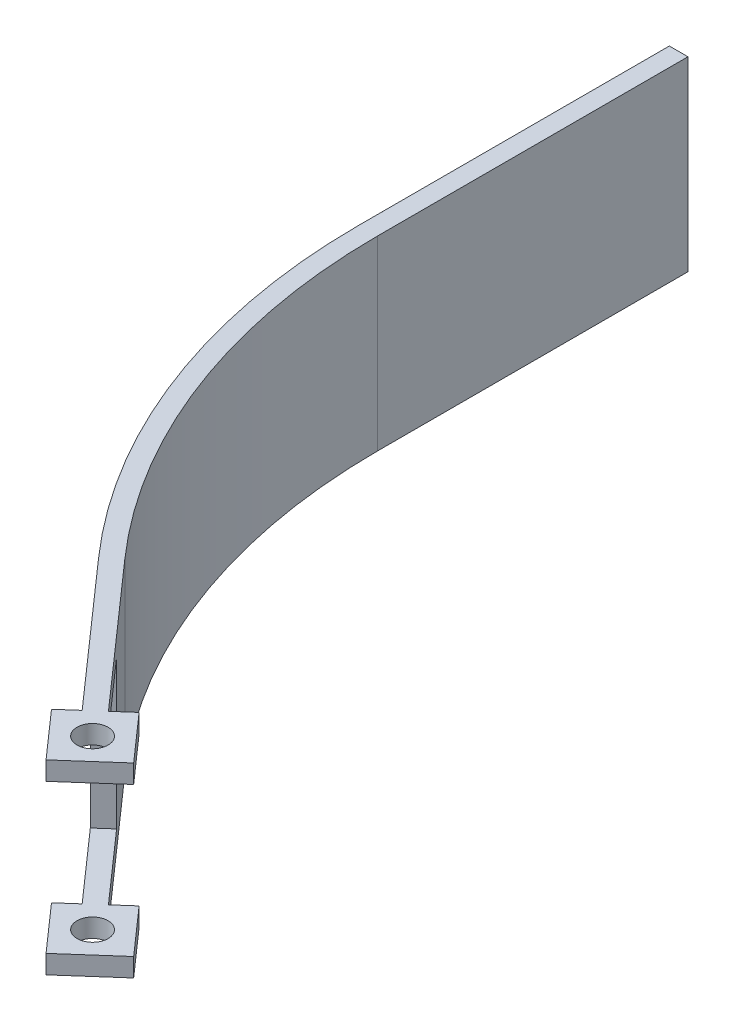
SolidWorks part; units mm, degrees
ref_plane "Face" through (0, 0, 0) normal (0, 0, 1) x (1, 0, 0)
ref_plane "Dessus" through (0, 0, 0) normal (0, 1, 0) x (1, 0, 0)
ref_plane "Droite" through (0, 0, 0) normal (1, 0, 0) x (0, 0, -1)
sketch "Esquisse1" plane through (0, 0, 0) normal (0, 1, 0) x (1, 0, 0)
  line L0 (0, 0) -> (0, 50)
  line L1 (0, 50) -> (3, 50)
  line L2 (3, 50) -> (3, 0)
  line L3 (25.5397, -67.5117) -> (27.7886, -65.526) construction
  line L4 (47.6449, -88.0144) -> (50.2686, -85.6978)
  line L5 (25.5397, -67.5117) -> (45.3961, -90)
  line L6 (27.7886, -65.526) -> (47.6449, -88.0144)
  line L7 (50.2686, -85.6978) -> (56.8874, -93.1939)
  line L8 (56.8874, -93.1939) -> (49.3913, -99.8127)
  line L9 (49.3913, -99.8127) -> (42.7725, -92.3166)
  line L10 (42.7725, -92.3166) -> (45.3961, -90)
  line L11 (46.0819, -96.0646) -> (53.578, -89.4458) construction
  arc A0 (0, 0) -> (25.5397, -67.5117) centre (102, 0) ccw
  arc A1 (3, 0) -> (27.7886, -65.526) centre (102, 0) ccw
  circle A2 centre (49.8299, -92.7552) radius 2.5
  dimension "D2" = 102
  dimension "D8" = 5
  dimension "D1" = 50
  dimension "D3" = 30
  dimension "D4" = 3
  dimension "D5" = 3
  dimension "D6" = 140
  dimension "D7" = 10
extrude "Extrusion1" add sketch "Esquisse1" along normal blind 30
sketch "Esquisse3" plane through (-21.7685, 0, 19.2208) normal (-0.7496, 0, 0.6619) x (0.6619, 0, 0.7496)
  line L0 (107.5117, 30) -> (107.5117, 0) construction
  line L1 (107.5117, 27) -> (82.5117, 27)
  line L2 (107.5117, 27) -> (107.5117, 3)
  line L3 (107.5117, 3) -> (82.5117, 3)
  line L4 (82.5117, 27) -> (82.5117, 3)
  line L5 (97.5117, 30) -> (107.5117, 30) construction
  line L6 (97.5117, 0) -> (107.5117, 0) construction
  dimension "D1" = 3
  dimension "D2" = 3
  dimension "D3" = 25
extrude "Extrusion2" cut sketch "Esquisse3" against normal through all
